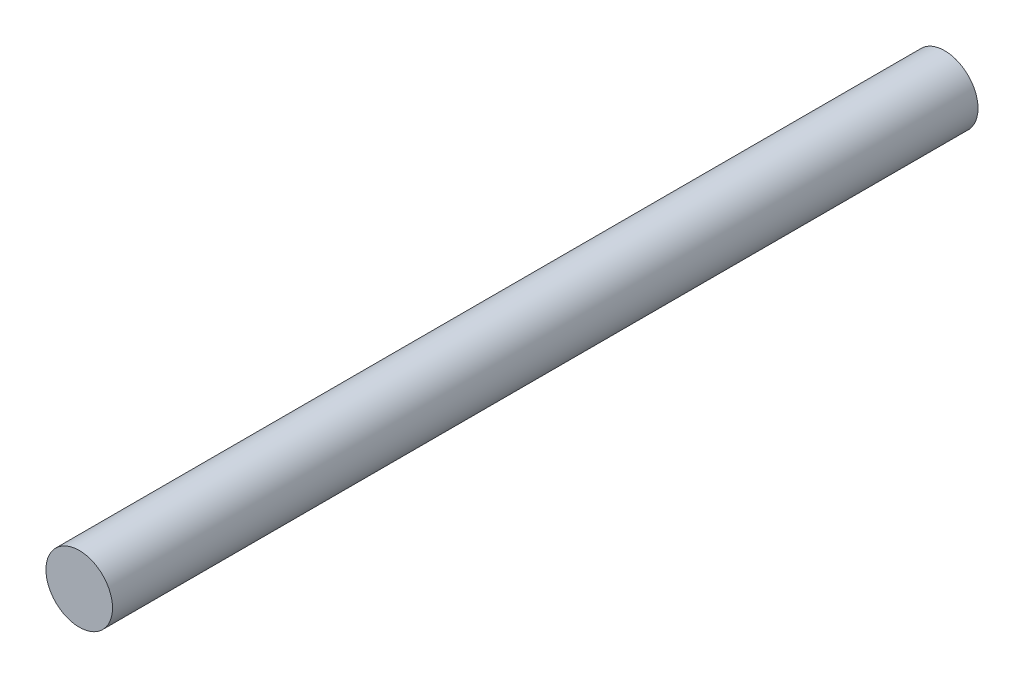
SolidWorks part; units mm, degrees
material "1023 Carbon Steel Sheet (SS)"
ref_plane "Front Plane" through (0, 0, 0) normal (0, 0, 1) x (1, 0, 0)
ref_plane "Top Plane" through (0, 0, 0) normal (0, 1, 0) x (1, 0, 0)
ref_plane "Right Plane" through (0, 0, 0) normal (1, 0, 0) x (0, 0, -1)
sketch "Sketch1" plane through (0, 0, 0) normal (0, 0, 1) x (1, 0, 0)
  circle A0 centre (0, 0) radius 6.35
  dimension "D1" = 12.7
extrude "Boss-Extrude1" add sketch "Sketch1" along normal mid plane 165.1
